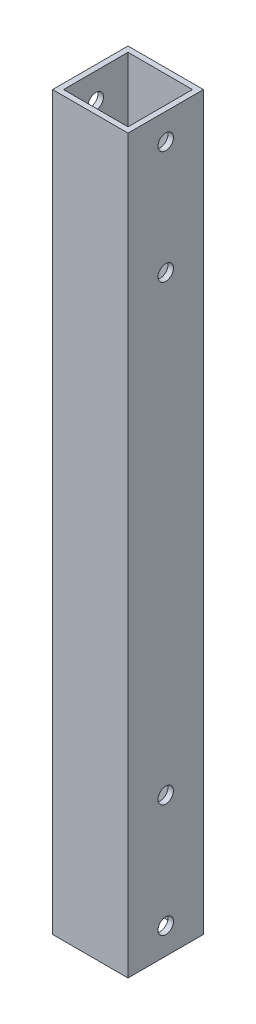
SolidWorks part; units mm, degrees
ref_plane "Front Plane" through (0, 0, 0) normal (0, 0, 1) x (1, 0, 0)
ref_plane "Top Plane" through (0, 0, 0) normal (0, 1, 0) x (1, 0, 0)
ref_plane "Right Plane" through (0, 0, 0) normal (1, 0, 0) x (0, 0, -1)
sketch "Sketch1" plane through (0, 0, 0) normal (0, 1, 0) x (1, 0, 0)
  line L0 (1.45, 18.55) -> (18.55, 18.55)
  line L1 (0, 0) -> (20, 0)
  line L2 (0, 0) -> (0, 20)
  line L3 (0, 20) -> (20, 20)
  line L4 (20, 0) -> (20, 20)
  line L5 (18.55, 1.45) -> (18.55, 18.55)
  line L6 (1.45, 1.45) -> (18.55, 1.45)
  line L7 (1.45, 1.45) -> (1.45, 18.55)
  dimension "D1" = 20
  dimension "D2" = 1.45
extrude "Boss-Extrude1" add sketch "Sketch1" along normal blind 194
sketch "Sketch2" plane through (0, 0, 0) normal (-1, 0, 0) x (0, 0, 1)
  line L0 (-20, 194) -> (-20, 0) construction
  line L1 (-20, 194) -> (0, 194) construction
  line L2 (-20, 0) -> (0, 0) construction
  circle A0 centre (-10, 187) radius 2.05
  circle A1 centre (-10, 157) radius 2.05
  circle A2 centre (-10, 37) radius 2.05
  circle A3 centre (-10, 7) radius 2.05
  dimension "D1" = 4.1
  dimension "D2" = 30
  dimension "D3" = 30
  dimension "D4" = 10
  dimension "D5" = 7
  dimension "D6" = 7
extrude "Cut-Extrude1" cut sketch "Sketch2" against normal through all
